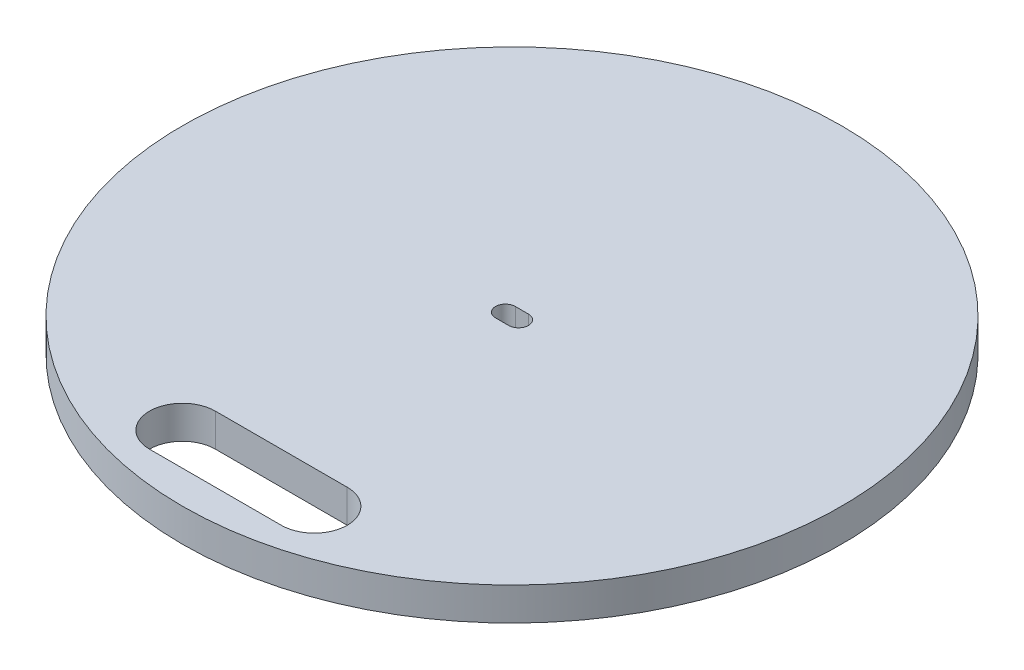
SolidWorks part; units mm, degrees
ref_plane "Front Plane" through (0, 0, 0) normal (0, 0, 1) x (1, 0, 0)
ref_plane "Top Plane" through (0, 0, 0) normal (0, 1, 0) x (1, 0, 0)
ref_plane "Right Plane" through (0, 0, 0) normal (1, 0, 0) x (0, 0, -1)
sketch "Sketch1" plane through (0, 0, 0) normal (0, 1, 0) x (1, 0, 0)
  circle A0 centre (0, 0) radius 50
  dimension "D1" = 100
extrude "Boss-Extrude1" add sketch "Sketch1" along normal blind 5 contours A0
sketch "Sketch3" plane through (0, 5, 0) normal (0, 1, 0) x (1, 0, 0)
  line L0 (-1, 0) -> (1, 0) construction
  line L3 (0, 50) -> (0, -50) construction
  line L4 (-1, 1.5) -> (1, 1.5)
  line L5 (-1, -1.5) -> (1, -1.5)
  circle A2 centre (0, 0) radius 50 construction
  arc A3 (-1, 1.5) -> (-1, -1.5) centre (-1, 0) ccw
  arc A4 (1, -1.5) -> (1, 1.5) centre (1, 0) ccw
  point P3 (0, 0)
  point P8 (-2.5, 0)
  point P9 (2.5, 0)
  point P16 (0, 1.5)
  point P17 (0, -1.5)
  dimension "D1" = 5
  dimension "D2" = 3
extrude "Cut-Extrude1" cut sketch "Sketch3" against normal through all
sketch "Sketch5" plane through (0, 5, 0) normal (0, 1, 0) x (1, 0, 0)
  line L0 (-10, -40) -> (10, -40) construction
  line L3 (-10, -35) -> (10, -35)
  line L4 (-10, -45) -> (10, -45)
  line L5 (0, 0) -> (0, -50) construction
  arc A2 (-10, -35) -> (-10, -45) centre (-10, -40) ccw
  arc A3 (10, -45) -> (10, -35) centre (10, -40) ccw
  circle A4 centre (0, 0) radius 50 construction
  point P2 (0, -40)
  point P12 (0, 0)
  dimension "D1" = 0
  dimension "D2" = 10
extrude "Cut-Extrude2" cut sketch "Sketch5" against normal through all
